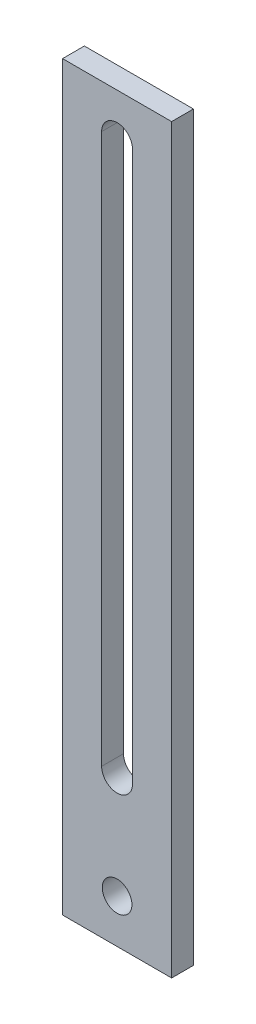
SolidWorks part; units mm, degrees
ref_plane "Front" through (0, 0, 0) normal (0, 0, 1) x (1, 0, 0)
ref_plane "Top" through (0, 0, 0) normal (0, 1, 0) x (1, 0, 0)
ref_plane "Right" through (0, 0, 0) normal (1, 0, 0) x (0, 0, -1)
sketch "Sketch1" plane through (0, 0, 0) normal (0, 0, 1) x (1, 0, 0)
  line L0 (7.9375, 101.6) -> (7.9375, 21.59) construction
  line L1 (0, 0) -> (15.875, 0)
  line L2 (0, 0) -> (0, 107.95)
  line L3 (0, 107.95) -> (15.875, 107.95)
  line L4 (15.875, 0) -> (15.875, 107.95)
  line L7 (7.9375, 0) -> (7.9375, 101.6) construction
  line L8 (10.1854, 101.6) -> (10.1854, 21.59)
  line L9 (5.6896, 101.6) -> (5.6896, 21.59)
  circle A2 centre (7.9375, 6.35) radius 2.159
  arc A3 (10.1854, 101.6) -> (5.6896, 101.6) centre (7.9375, 101.6) ccw
  arc A4 (5.6896, 21.59) -> (10.1854, 21.59) centre (7.9375, 21.59) ccw
  point P7 (7.9375, 61.595)
  point P14 (0, 0)
  point P15 (0, 0)
  dimension "D3" = 4.318
  dimension "D4" = 2.2479
  dimension "D1" = 107.95
  dimension "D2" = 15.875
  dimension "D5" = 15.24
  dimension "D6" = 6.35
  dimension "D7" = 6.35
extrude "Boss-Extrude1" add sketch "Sketch1" along normal blind 3.175
